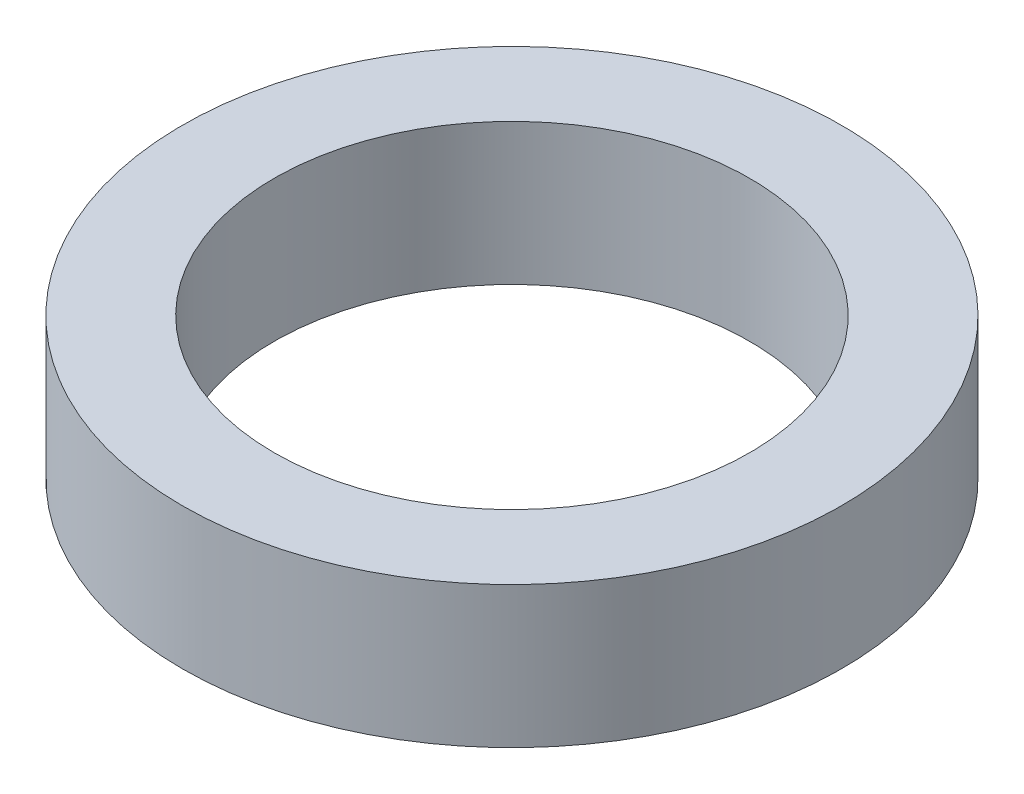
SolidWorks part; units mm, degrees
ref_plane "Front Plane" through (0, 0, 0) normal (0, 0, 1) x (1, 0, 0)
ref_plane "Top Plane" through (0, 0, 0) normal (0, 1, 0) x (1, 0, 0)
ref_plane "Right Plane" through (0, 0, 0) normal (1, 0, 0) x (0, 0, -1)
sketch "Sketch1" plane through (0, 0, 0) normal (0, 1, 0) x (1, 0, 0)
  circle A0 centre (0, 0) radius 3.5
  circle A1 centre (0, 0) radius 2.525
  dimension "D1" = 7
  dimension "D2" = 5.05
extrude "Boss-Extrude1" add sketch "Sketch1" along normal blind 1.5
